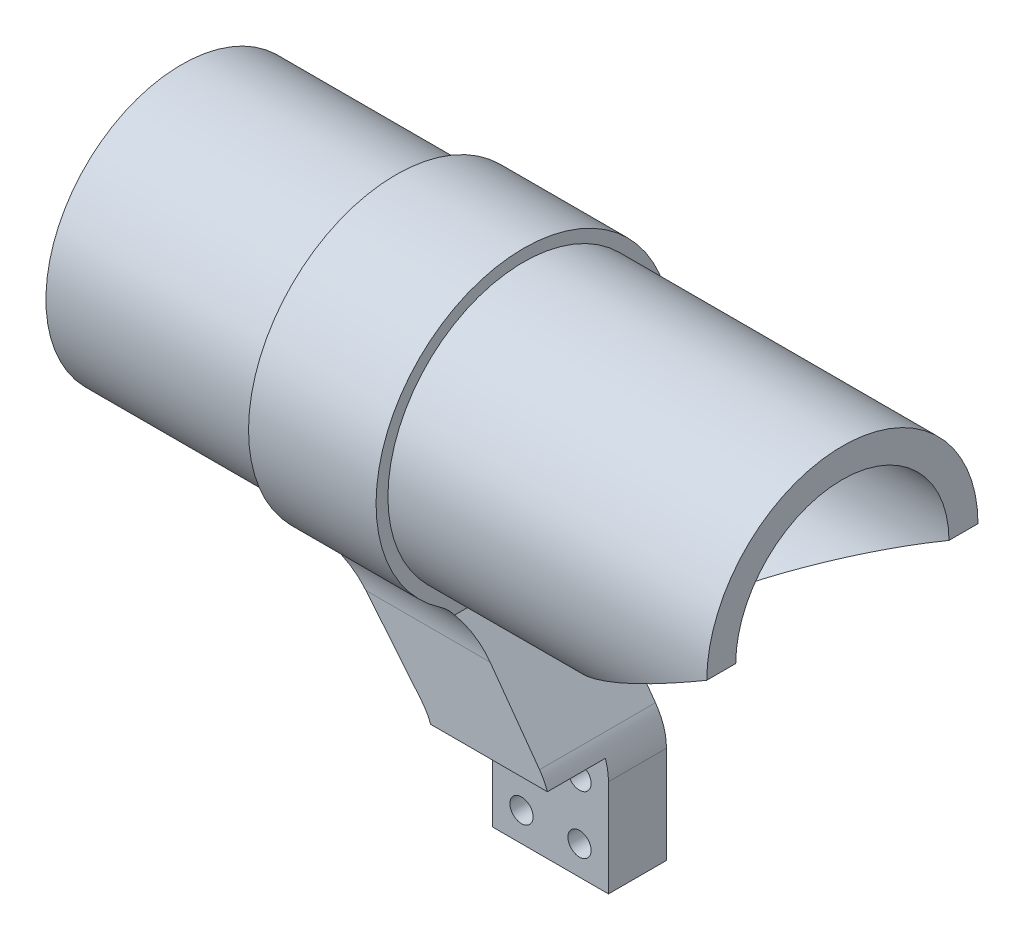
SolidWorks part; units mm, degrees
ref_plane "Alzado" through (0, 0, 0) normal (0, 0, 1) x (1, 0, 0)
ref_plane "Planta" through (0, 0, 0) normal (0, 1, 0) x (1, 0, 0)
ref_plane "Vista lateral" through (0, 0, 0) normal (1, 0, 0) x (0, 0, -1)
sketch "Croquis1" plane through (0, 0, 0) normal (1, 0, 0) x (0, 0, -1)
  circle A0 centre (0, 0) radius 18.4
  circle A1 centre (0, 0) radius 23.4
  dimension "D1" = 36.8
  dimension "D2" = 5
extrude "Saliente-Extruir1" add sketch "Croquis1" along normal blind 114
sketch "Croquis2" plane through (0, 0, 0) normal (-1, 0, 0) x (0, 0, 1)
  circle A0 centre (0, 0) radius 7.5
  circle A1 centre (0, 0) radius 23.4
  circle A2 centre (-11.1381, -8.4819) radius 1.25
  circle A3 centre (8.4819, -11.1381) radius 1.25
  circle A4 centre (11.1381, 8.4819) radius 1.25
  circle A5 centre (-8.4819, 11.1381) radius 1.25
  dimension "D1" = 2.5
  dimension "D2" = 46.8
  dimension "D3" = 15
extrude "Saliente-Extruir2" add sketch "Croquis2" against normal blind 5
sketch "Croquis4" plane through (0, 0, 0) normal (0, 0, 1) x (1, 0, 0)
  line L0 (114, 0.1) -> (74, -23.4)
  line L1 (0, -23.4) -> (114, -23.4) construction
  line L2 (74, -23.4) -> (114, -23.4)
  line L3 (114, -23.4) -> (114, 0.1)
  dimension "D1" = 23.5
  dimension "D2" = 40
extrude "Cortar-Extruir1" cut sketch "Croquis4" against normal mid plane 47
sketch "Croquis6" plane through (5, 0, 0) normal (1, 0, 0) x (0, 0, -1)
  circle A0 centre (0, 0) radius 11.5
  dimension "D1" = 23
extrude "Cortar-Extruir2" cut sketch "Croquis6" against normal blind 2.5
sketch "Croquis9" plane through (0, 0, 0) normal (0, 0, 1) x (1, 0, 0)
  line L0 (73.6502, -43.6934) -> (73.6502, -63.6934)
  line L1 (73.6502, -63.6934) -> (53.6502, -63.6934)
  line L2 (53.6502, -63.6934) -> (53.6502, -43.6934)
  line L5 (73.6502, -43.6934) -> (59, -23.4)
  line L6 (0, -23.4) -> (74, -23.4) construction
  line L7 (59, -23.4) -> (37, -23.4)
  line L8 (37, -23.4) -> (53.6502, -43.6934)
  line L9 (73.6502, -43.6934) -> (53.6502, -63.6934) construction
  line L10 (73.6502, -63.6934) -> (53.6502, -43.6934) construction
  circle A0 centre (58.6502, -48.6934) radius 2
  circle A2 centre (58.6502, -58.6934) radius 2
  circle A3 centre (68.6502, -58.6934) radius 2
  circle A4 centre (68.6502, -48.6934) radius 2
  point P10 (63.6502, -53.6934)
  dimension "D6" = 4
  dimension "D1" = 20
  dimension "D2" = 20
  dimension "D3" = 20
  dimension "D4" = 22
  dimension "D5" = 15
  dimension "D7" = 5
extrude "Saliente-Extruir3" add sketch "Croquis9" along normal mid plane 20 separate body
fillet "Redondeo3" radius 10 2 edges at (53.6502, -43.6934, 0) (73.6502, -43.6934, 0)
sketch "Croquis10" plane through (0, 0, 10) normal (0, 0, 1) x (1, 0, 0)
  line L0 (73.6502, -63.6934) -> (73.6502, -46.9258) construction
  line L4 (73.6502, -43.6934) -> (73.6502, -63.6934)
  line L5 (73.6502, -43.6934) -> (50.4958, -43.6934)
  line L6 (50.4958, -43.6934) -> (50.4958, -63.6934)
  line L7 (53.6502, -63.6934) -> (73.6502, -63.6934) construction
  line L8 (50.4958, -63.6934) -> (73.6502, -63.6934)
  point P0 (63.6502, -53.6934)
extrude "Cortar-Extruir3" cut sketch "Croquis10" against normal blind 10
ref_plane "Plano1" through (37, 0, 0) normal (1, 0, 0) x (0, 0, -1)
sketch "Croquis11" plane through (37, 0, 0) normal (1, 0, 0) x (0, 0, -1)
  line L0 (-10, -23.4) -> (10, -23.4)
  arc A0 (10, -23.4) -> (-10, -23.4) centre (0, 0) ccw
extrude "Saliente-Extruir4" add sketch "Croquis11" along normal blind 22
fillet "Redondeo1" radius 10 2 edges at (48, -23.4, -10) (48, -23.4, 10)
sketch "Croquis12" plane through (37, 0, 0) normal (-1, 0, 0) x (0, 0, 1)
  circle A0 centre (0, 0) radius 18.4
  dimension "D1" = 36.8
extrude "Cortar-Extruir4" cut sketch "Croquis12" against normal through all
